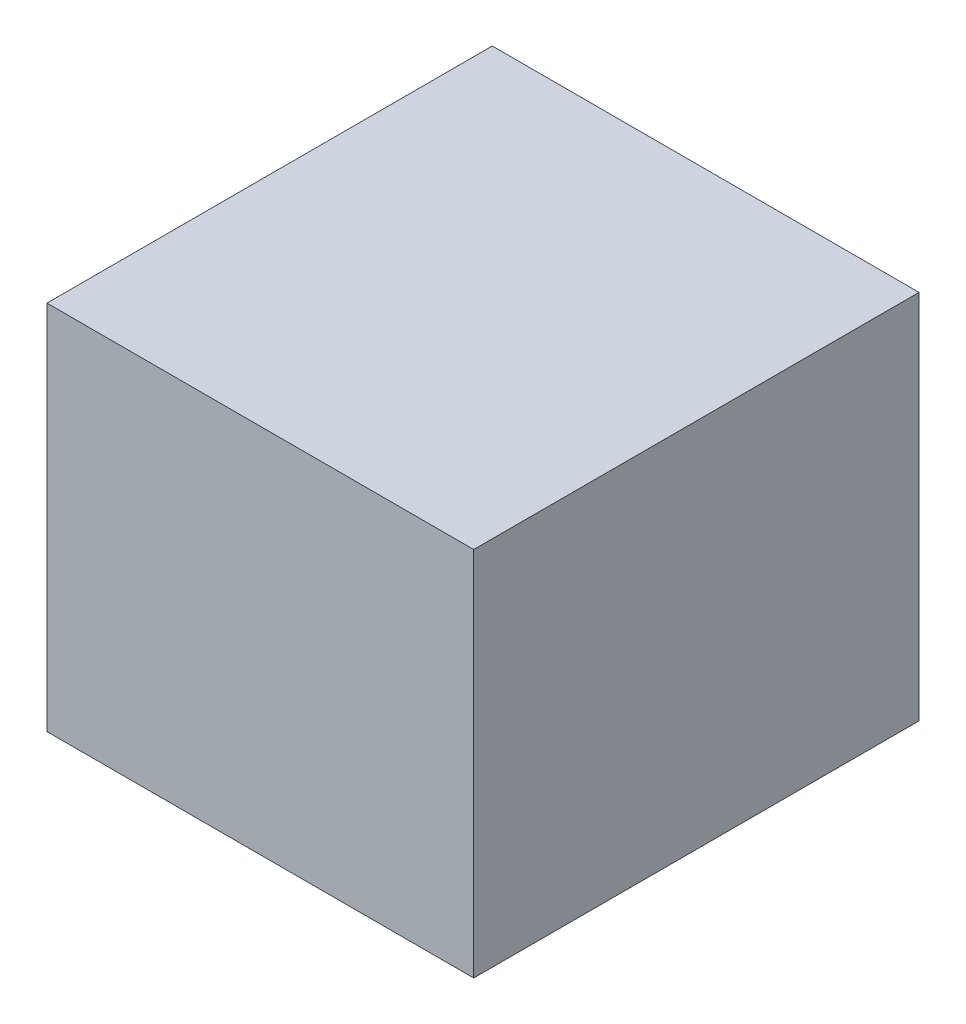
SolidWorks part; units mm, degrees
ref_plane "前基準面" through (0, 0, 0) normal (0, 0, 1) x (1, 0, 0)
ref_plane "上基準面" through (0, 0, 0) normal (0, 1, 0) x (1, 0, 0)
ref_plane "右基準面" through (0, 0, 0) normal (1, 0, 0) x (0, 0, -1)
sketch "草圖1" plane through (0, 0, 0) normal (1, 0, 0) x (0, 0, -1)
  line L1 (-300, 250) -> (300, 250)
  line L2 (-300, 250) -> (-300, -250)
  line L3 (-300, -250) -> (300, -250)
  line L4 (300, 250) -> (300, -250)
  line L5 (-300, 250) -> (300, -250) construction
  line L6 (-300, -250) -> (300, 250) construction
  point P0 (0, 0)
  dimension "D1" = 500
  dimension "D2" = 600
extrude "填料-伸長1" add sketch "草圖1" along normal mid plane 575
